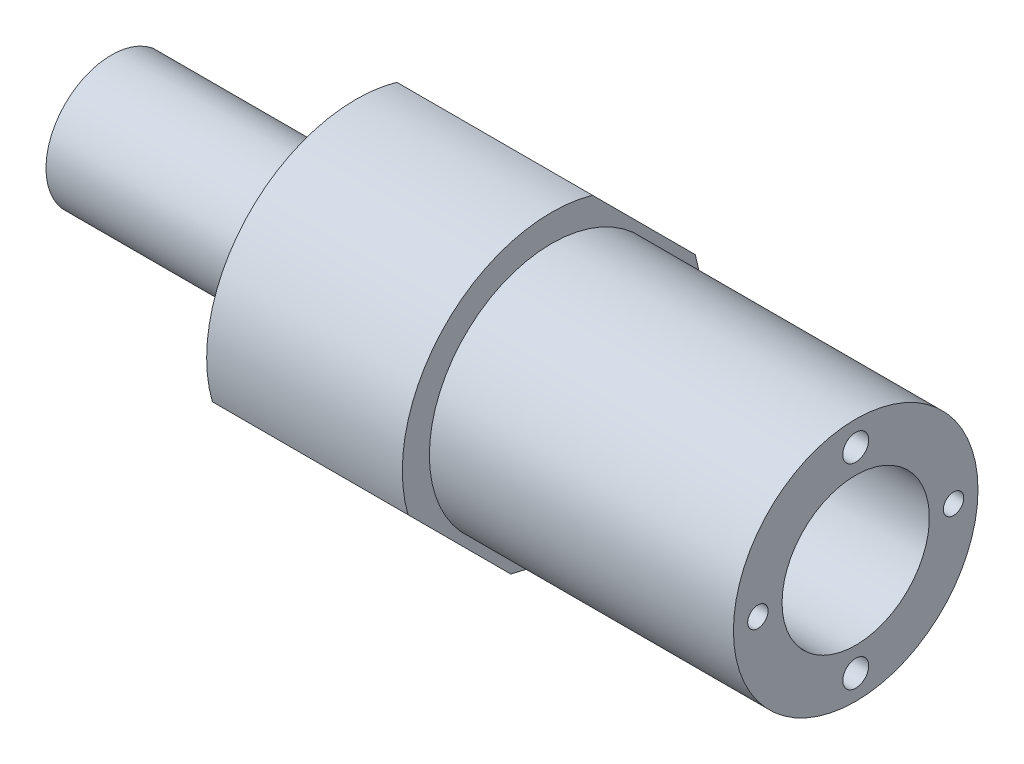
SolidWorks part; units mm, degrees
material "AISI 304"
ref_plane "Front Plane" through (0, 0, 0) normal (0, 0, 1) x (1, 0, 0)
ref_plane "Top Plane" through (0, 0, 0) normal (0, 1, 0) x (1, 0, 0)
ref_plane "Right Plane" through (0, 0, 0) normal (1, 0, 0) x (0, 0, -1)
sketch "Sketch3" plane through (0, 0, 0) normal (0, 0, 1) x (1, 0, 0)
  line L0 (-58.5481, 189.9573) -> (284.033, 189.9573) construction
  line L2 (213.4012, -189.6279) -> (558.7345, -189.6279) construction
  line L4 (227.3705, -148.5737) -> (308.4812, -148.5737) construction
  line L25 (233.6593, -146.8737) -> (233.6593, -145.6737)
  line L26 (233.6593, -145.6737) -> (300.6593, -145.6737)
  line L27 (300.6593, -145.6737) -> (300.6593, -148.1737)
  line L28 (300.6593, -148.1737) -> (284.5593, -148.1737)
  line L29 (284.5593, -148.1737) -> (284.5593, -146.8713)
  line L30 (284.5593, -146.8713) -> (233.6593, -146.8737)
  line L31 (251.8003, -145.6737) -> (251.8003, -143.5284)
  line L32 (251.8003, -143.5284) -> (253.3698, -143.5284)
  line L33 (253.3698, -143.5284) -> (253.3698, -140.805)
  line L34 (253.3698, -140.805) -> (248.9846, -140.805)
  line L35 (248.9846, -140.805) -> (248.9846, -145.6737)
  line L36 (248.9846, -145.6737) -> (251.8003, -145.6737)
  line L38 (248.9846, -141.405) -> (235.8631, -141.405)
  line L39 (235.8631, -141.405) -> (235.8631, -143.2393)
  line L40 (235.8631, -143.2393) -> (234.2014, -143.2393)
  line L41 (234.2014, -143.2393) -> (234.2014, -143.5284)
  line L42 (234.2014, -143.5284) -> (233.6472, -143.5284)
  line L43 (233.6472, -143.5284) -> (233.6472, -143.9438)
  line L44 (233.6472, -143.9438) -> (231.1087, -143.9438)
  line L45 (231.1087, -143.9438) -> (231.1087, -142.3222)
  line L46 (231.1087, -142.3222) -> (224.7848, -142.3222)
  line L47 (224.7848, -142.3222) -> (224.7848, -145.1901)
  line L48 (224.7848, -145.1901) -> (223.8155, -145.1901)
  line L49 (223.8155, -145.1901) -> (223.8155, -144.601)
  line L50 (223.8155, -144.601) -> (224.3882, -144.601)
  line L51 (224.3882, -144.601) -> (224.3882, -144.3605)
  line L52 (224.3882, -144.3605) -> (222.6328, -144.3605)
  line L53 (222.6328, -144.3605) -> (222.6328, -142.6581)
  line L54 (222.6328, -142.6581) -> (212.7719, -142.6581)
  line L55 (212.7719, -142.6581) -> (212.7719, -143.133)
  line L56 (212.7719, -143.133) -> (211.9894, -143.133)
  line L57 (211.9894, -143.133) -> (211.9894, -143.5093)
  line L58 (211.9894, -143.5093) -> (209.8233, -143.5093)
  line L59 (209.8233, -143.5093) -> (209.8233, -146.4907)
  line L60 (209.8233, -146.4907) -> (209.8233, -146.8737)
  line L61 (209.8233, -146.8737) -> (210.2598, -146.8737)
  line L62 (210.2598, -146.8737) -> (210.2598, -147.3348)
  line L63 (210.2598, -147.3348) -> (222.6328, -147.3348)
  line L64 (222.6328, -147.3348) -> (222.6328, -147.7807)
  line L65 (222.6328, -147.7807) -> (233.6593, -147.7807)
  line L66 (233.6593, -147.7807) -> (233.6593, -145.6737)
  line L67 (248.9846, -145.6737) -> (233.6593, -145.6737)
  line L68 (233.6593, -145.6737) -> (248.9846, -145.6737)
  line L69 (209.8233, -145.6737) -> (205.1515, -145.6737)
  line L70 (205.1515, -145.6737) -> (205.1515, -140.5475)
  line L71 (205.1515, -140.5475) -> (212.7719, -140.5475)
  line L72 (212.7719, -140.5475) -> (212.7719, -143.133)
  line L73 (211.9894, -143.133) -> (211.9894, -143.5093)
  line L74 (209.8233, -143.5093) -> (209.8233, -145.6737)
  line L75 (205.1515, -145.1901) -> (167.9786, -145.1901)
  line L76 (167.9786, -145.1901) -> (167.9786, -140.5475)
  line L83 (259.2786, -139.5374) -> (208.579, -139.5374)
  line L84 (208.579, -139.5374) -> (208.579, -140.5475)
  line L85 (208.579, -140.5475) -> (205.1515, -140.5475)
  line L86 (205.1515, -145.1901) -> (205.1515, -140.5475)
  line L87 (238.4273, -133.5737) -> (238.4273, -129.7144)
  line L88 (238.4273, -129.7144) -> (264.4186, -129.7144)
  line L89 (264.4186, -141.0487) -> (264.4186, -129.7144)
  line L90 (264.4186, -141.0487) -> (261.9145, -141.0487)
  line L91 (238.4273, -133.5737) -> (259.2786, -133.5737)
  line L92 (259.2786, -133.5737) -> (259.2786, -139.5374)
  line L93 (259.2786, -139.5374) -> (259.2786, -140.7794)
  line L94 (259.2786, -140.7794) -> (261.9145, -140.7794)
  line L95 (250.6852, -139.5374) -> (250.6852, -140.805)
  line L96 (253.3698, -143.5284) -> (259.2786, -143.5284)
  line L97 (259.2786, -143.5284) -> (259.2786, -140.7794)
  line L98 (259.2786, -143.5284) -> (302.0274, -143.5284)
  line L99 (302.0274, -143.5284) -> (302.0274, -145.1901)
  line L100 (302.0274, -145.1901) -> (304.5325, -145.1901)
  line L101 (304.5325, -145.1901) -> (304.5325, -141.0487)
  line L102 (304.5325, -141.0487) -> (264.4186, -141.0487)
  line L103 (238.4273, -133.5737) -> (221.9786, -133.5737)
  line L104 (161.2028, -147.3348) -> (161.2028, -146.4907)
  line L105 (161.2028, -146.4907) -> (209.8233, -146.4907)
  line L106 (209.8233, -146.8737) -> (210.2598, -146.8737)
  line L107 (210.2598, -147.3348) -> (222.6328, -147.3348)
  line L108 (210.2598, -147.3348) -> (161.2028, -147.3348)
  line L109 (209.8233, -146.4907) -> (209.8233, -146.8737)
  line L110 (209.8233, -146.8737) -> (210.2598, -146.8737)
  line L111 (210.2598, -146.8737) -> (210.2598, -147.3348)
  line L112 (261.9145, -141.0487) -> (261.9145, -140.7794)
  line L114 (197.9786, -130.257) -> (221.9786, -130.257)
  line L115 (221.9786, -130.257) -> (221.9786, -133.5737)
  line L116 (197.9786, -130.257) -> (197.9786, -140.5475)
  line L117 (197.9786, -140.5475) -> (167.9786, -140.5475)
  dimension "D1" = 1.7
  dimension "D2" = 0.4
  dimension "D3" = 2.5
  dimension "D4" = 67
  dimension "D5" = 16.1
  dimension "D6" = 24
  dimension "D7" = 30
  dimension "D8" = 15
revolve "Revolve1" add sketch "Sketch3" angle 360 about L4
ref_axis "Axis1" through (205.1515, -148.5737, 0) along (-1, 0, 0)
ref_plane "Plane1" through (0, -148.5737, 0) normal (0, 1, 0) x (1, 0, 0)
sketch "Sketch8" plane through (259.2786, 0, 0) normal (1, 0, 0) x (0, 0, -1)
  circle A1 centre (0, -136.5737) radius 1.5875
  circle A3 centre (0, -160.5737) radius 1.5875
  circle A4 centre (0, -148.5737) radius 12 construction
  point P9 (0, -148.5737)
  dimension "D1" = 24
  dimension "D4" = 0
extrude "Cut-Extrude1" cut sketch "Sketch8" against normal up to next
sketch "Sketch9" plane through (259.2786, 0, 0) normal (1, 0, 0) x (0, 0, -1)
  circle A0 centre (0, -148.5737) radius 12 construction
  dimension "D1" = 24
hole_wizard "Tap Drill for M3 Tap2" positions "Sketch11" profile "Sketch12" hole size "M3" standard "ISO"
sketch "Sketch11" plane through (259.2786, 0, 0) normal (1, 0, 0) x (0, 0, -1)
  circle A0 centre (0, -148.5737) radius 12 construction
  point P0 (-12, -148.5737)
  point P4 (12, -148.5737)
sketch "Sketch12" plane through (259.2786, -148.5737, 12) normal (0, 1, 0) x (0, 0, -1)
  line L0 (0, 0) -> (0, 6.7511)
  line L1 (0, 6.7511) -> (1.25, 6)
  line L2 (1.25, 6) -> (1.25, 0)
  line L5 (1.25, 0) -> (0, 0)
  line L10 (0, 6.7511) -> (-1.25, 6) construction
  line L11 (0, -6.35) -> (0, 107.95) construction
  dimension "Hole Dia." = 2.5
  dimension "Hole Depth" = 6
  dimension "Drill Angle" = 118
hole_wizard "Tap Drill for M4 Tap1" positions "Sketch15" profile "Sketch14" hole size "M4" standard "ISO"
sketch "Sketch15" plane through (197.9786, 0, 0) normal (-1, 0, 0) x (0, 0, 1)
  circle A0 centre (0, -148.5737) radius 12 construction
  point P0 (-12, -148.5737)
  point P4 (12, -148.5737)
sketch "Sketch14" plane through (197.9786, -148.5737, -12) normal (0, 1, 0) x (0, 0, 1)
  line L0 (0, 0) -> (0, 10.9914)
  line L1 (0, 10.9914) -> (1.65, 10)
  line L2 (1.65, 10) -> (1.65, 0)
  line L5 (1.65, 0) -> (0, 0)
  line L10 (0, 10.9914) -> (-1.65, 10) construction
  line L11 (0, -6.35) -> (0, 107.95) construction
  dimension "Hole Dia." = 3.3
  dimension "Hole Depth" = 10
  dimension "Drill Angle" = 118
sketch "Sketch16" plane through (197.9786, 0, 0) normal (-1, 0, 0) x (0, 0, 1)
  line L0 (-1.6371, -127.5834) -> (-21.6158, -147.5621)
  line L1 (-21.6158, -147.5621) -> (-21.6158, -136.774)
  line L2 (24.0698, -155.6354) -> (24.0698, -147.1313)
  line L3 (24.0698, -147.1313) -> (1.9835, -169.2176)
  line L4 (1.9835, -169.2176) -> (24.0698, -155.6354)
  line L5 (-21.6158, -136.774) -> (-1.6371, -127.5834)
  dimension "D1" = 45
  dimension "D2" = 16
  dimension "D3" = 16
extrude "Cut-Extrude2" cut sketch "Sketch16" against normal blind 30
hole_wizard "Tap Drill for M5 Tap1" positions "Sketch17" profile "Sketch18" hole size "M5" standard "ISO"
sketch "Sketch17" plane through (0, -62.9731, 62.9731) normal (0, 0.7071, -0.7071) x (-1, 0, 0)
  line L0 (-205.1515, -105.0575) -> (-167.9786, -105.0575) construction
  line L1 (-221.9786, -96.141) -> (-221.9786, -113.9739) construction
  point P0 (-209.9786, -105.0575)
  dimension "D1" = 12
sketch "Sketch18" plane through (209.9786, -137.26, -11.3137) normal (1, 0, 0) x (0, 0.7071, 0.7071)
  line L0 (0, 0) -> (0, 5.2618)
  line L1 (0, 5.2618) -> (2.1, 4)
  line L2 (2.1, 4) -> (2.1, 0)
  line L5 (2.1, 0) -> (0, 0)
  line L10 (0, 5.2618) -> (-2.1, 4) construction
  line L11 (0, -6.35) -> (0, 107.95) construction
  dimension "Hole Dia." = 4.2
  dimension "Hole Depth" = 4
  dimension "Drill Angle" = 118
pattern_circular "CirPattern1" count 2 over 360 about axis through (205.1515, -148.5737, 0) along (-1, 0, 0) of "Tap Drill for M5 Tap1"
sketch "Sketch19" plane through (208.579, 0, 0) normal (1, 0, 0) x (0, 0, -1)
  line L0 (0, -148.5737) -> (5.5861, -142.9876) construction
  line L1 (0, -148.5737) -> (0, -140.5475) construction
  circle A1 centre (5.5861, -142.9876) radius 0.8
  circle A2 centre (0, -148.5737) radius 8.0262 construction
  dimension "D1" = 45
extrude "Cut-Extrude3" cut sketch "Sketch19" against normal up to next
